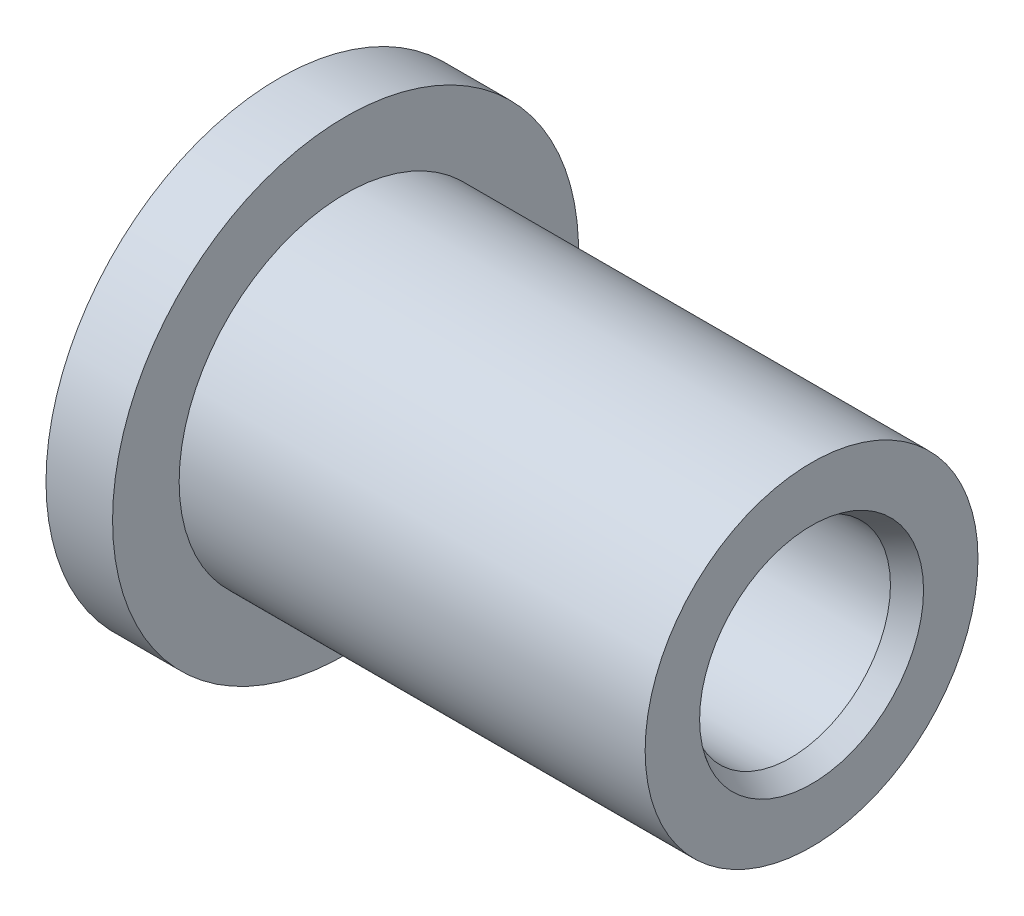
SolidWorks part; units mm, degrees
material "Brass"
ref_plane "Front Plane" through (0, 0, 0) normal (0, 0, 1) x (1, 0, 0)
ref_plane "Top Plane" through (0, 0, 0) normal (0, 1, 0) x (1, 0, 0)
ref_plane "Right Plane" through (0, 0, 0) normal (1, 0, 0) x (0, 0, -1)
sketch "Sketch1" plane through (0, 0, 0) normal (0, 0, 1) x (1, 0, 0)
  line L0 (0, 2.3812) -> (0, 5.5562)
  line L1 (0, 5.5562) -> (1.5875, 5.5562)
  line L2 (1.5875, 5.5562) -> (1.5875, 3.9688)
  line L3 (1.5875, 3.9688) -> (12.7, 3.9688)
  line L4 (12.7, 3.9688) -> (12.7, 2.3812)
  line L5 (12.7, 2.3812) -> (0, 2.3812)
  line L6 (0, 0) -> (22.026, 0) construction
  dimension "D1" = 4.7625
  dimension "D2" = 7.9375
  dimension "D3" = 11.1125
  dimension "D4" = 1.5875
  dimension "D5" = 12.7
revolve "Revolve1" add sketch "Sketch1" angle 360 about L6
chamfer "Chamfer1" distance 0.5 angle 30 2 edges at (12.7, 0, 2.3812) (0, 0, 2.3812)
